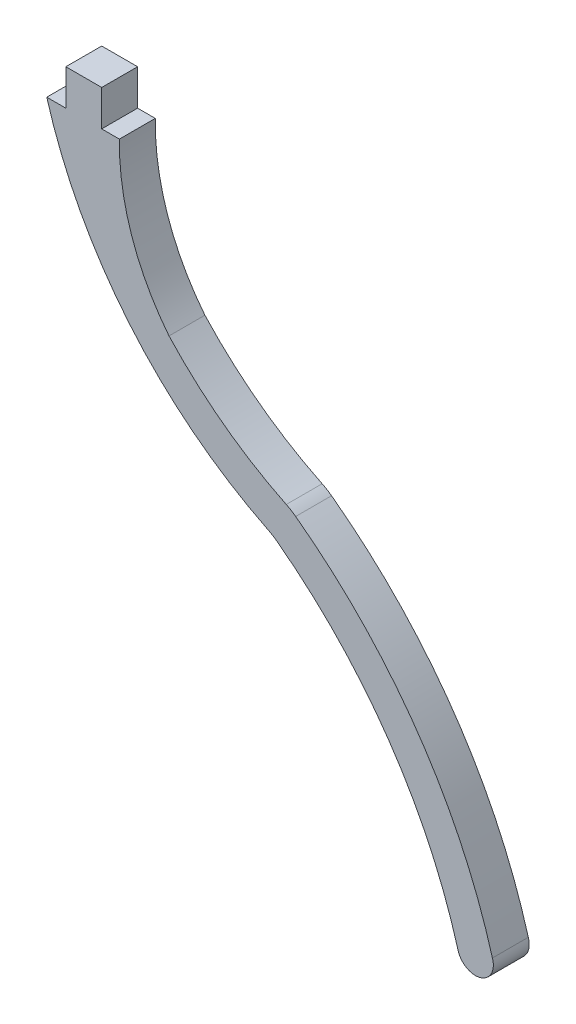
SolidWorks part; units mm, degrees
ref_plane "Front Plane" through (0, 0, 0) normal (0, 0, 1) x (1, 0, 0)
ref_plane "Top Plane" through (0, 0, 0) normal (0, 1, 0) x (1, 0, 0)
ref_plane "Right Plane" through (0, 0, 0) normal (1, 0, 0) x (0, 0, -1)
sketch "Sketch1" plane through (0, 0, 0) normal (0, 0, 1) x (1, 0, 0)
  line L0 (3.2055, 0) -> (3.2055, 1.524)
  line L1 (3.2055, 1.524) -> (4.7295, 1.524)
  line L2 (4.7295, 1.524) -> (4.7295, 0)
  line L3 (4.7295, 0) -> (5.4804, 0)
  line L4 (3.2055, 0) -> (2.396, 0)
  line L6 (4.562, -1.524) -> (4.562, -1.524)
  line L7 (4.562, -1.524) -> (4.562, -1.524)
  line L8 (4.562, -1.524) -> (4.562, -1.524)
  line L9 (4.562, -1.524) -> (4.562, -1.524)
  line L10 (4.562, -1.524) -> (5.4804, -1.524) construction
  arc A0 (2.396, 0) -> (11.7847, -11.2073) centre (19.8543, 5.0891) ccw
  arc A1 (12.1823, -11.4521) -> (19.8543, -22.6123) centre (-0.559, -28.4282) cw
  arc A2 (7.5877, -6.1855) -> (12.5663, -9.8933) centre (19.8543, 5.0891) ccw
  arc A3 (12.9652, -10.135) -> (21.32, -22.1947) centre (-0.559, -28.4282) cw
  arc A4 (5.4804, 0) -> (7.5877, -6.1855) centre (15.1605, -0.1539) ccw
  arc A5 (21.32, -22.1947) -> (19.8543, -22.6123) centre (20.5975, -22.4399) cw
  arc A6 (4.562, -1.524) -> (12.7638, -9.9878) centre (19.8543, 5.0891) ccw construction
  arc A7 (2.396, 0) -> (11.9818, -11.3035) centre (19.8543, 5.0891) ccw construction
  arc A8 (11.9818, -11.3035) -> (19.8543, -22.6123) centre (-0.559, -28.4282) cw construction
  arc A9 (11.7847, -11.2073) -> (12.1823, -11.4521) centre (10.6576, -13.4836) cw
  arc A10 (12.7638, -9.9878) -> (21.32, -22.1947) centre (-0.559, -28.4282) cw construction
  arc A11 (12.5663, -9.8933) -> (12.9652, -10.135) centre (11.4552, -12.1774) cw
  dimension "D2" = 2.54
  dimension "D1" = 1.524
extrude "Boss-Extrude1" add sketch "Sketch1" along normal blind 1.524 contours A11 A2 A4 L3 L2 L1 L0 L4 A0 A9 A1 A5 A3
